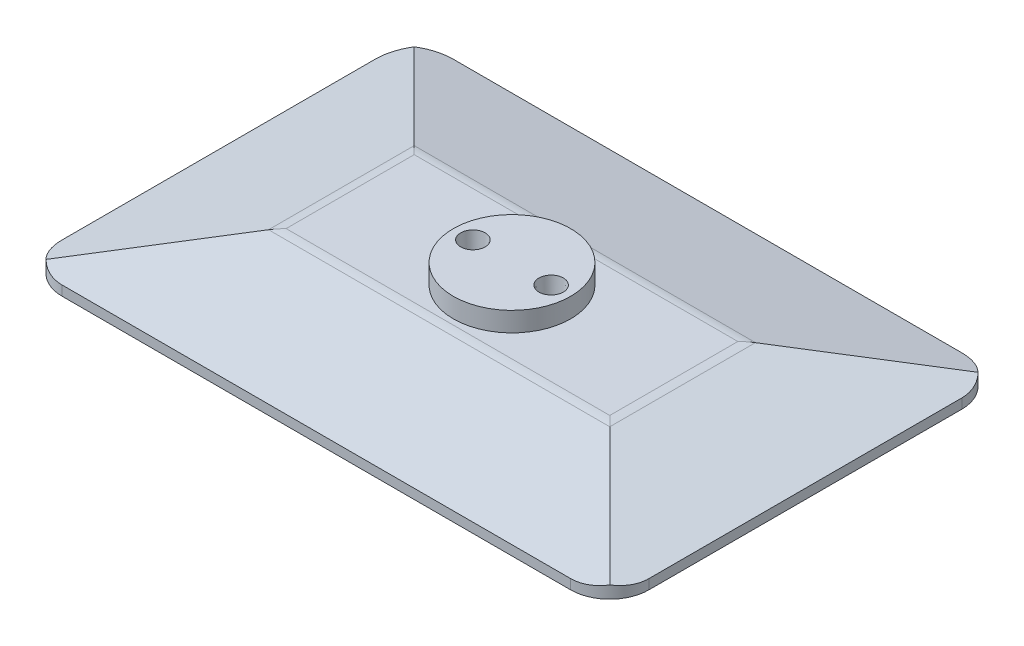
SolidWorks part; units mm, degrees
ref_plane "前视基准面" through (0, 0, 0) normal (0, 0, 1) x (1, 0, 0)
ref_plane "上视基准面" through (0, 0, 0) normal (0, 1, 0) x (1, 0, 0)
ref_plane "右视基准面" through (0, 0, 0) normal (1, 0, 0) x (0, 0, -1)
other "Configuration Table"
sketch "草图1" plane through (0, 0, 0) normal (0, 1, 0) x (1, 0, 0)
  line L0 (-48.5913, -10.2137) -> (-40.6154, -10.2137) construction
  line L1 (-33.5732, -10.2137) -> (-35.5732, -10.2137) construction
  line L2 (5.9754, 18.7871) -> (5.9754, 46.3845) construction
  line L3 (5.9754, 9.5066) -> (5.9754, -30.4934) construction
  line L5 (-24.0246, 9.7863) -> (35.9754, 9.7863)
  line L6 (-24.0246, 9.7863) -> (-24.0246, -30.2137)
  line L7 (-24.0246, -30.2137) -> (35.9754, -30.2137)
  line L8 (35.9754, 9.7863) -> (35.9754, -30.2137)
  line L9 (-24.0246, 9.7863) -> (35.9754, -30.2137) construction
  line L10 (-24.0246, -30.2137) -> (35.9754, 9.7863) construction
  point P8 (5.9754, -10.2137)
  dimension "D1" = 60
  dimension "D2" = 40
extrude "凸台-拉伸1" add sketch "草图1" along normal blind 1
sketch "草图2" plane through (0, 1, 0) normal (0, 1, 0) x (1, 0, 0)
  line L4 (35.9754, -30.2137) -> (35.9754, 9.7863)
  line L5 (35.9754, 9.7863) -> (-24.0246, 9.7863)
  line L6 (-24.0246, 9.7863) -> (-24.0246, -30.2137)
  line L7 (-24.0246, -30.2137) -> (35.9754, -30.2137)
  line L8 (35.9754, -30.2137) -> (35.9754, 9.7863)
  line L9 (35.9754, 9.7863) -> (-24.0246, 9.7863)
  line L10 (-24.0246, 9.7863) -> (-24.0246, -30.2137)
  line L11 (-24.0246, -30.2137) -> (35.9754, -30.2137)
  dimension "D1" = 0
extrude "凸台-拉伸2" add sketch "草图2" along normal blind 3 draft 77
fillet "圆角1" radius 4 4 edges at (-24.0246, 0.5, -9.7863) (35.9754, 0.5, -9.7863) (35.9754, 0.5, 30.2137) (-24.0246, 0.5, 30.2137)
sketch "草图3" plane through (0, 4, 0) normal (0, 1, 0) x (1, 0, 0)
  line L1 (5.9754, -16.2137) -> (5.9754, -4.2137) construction
  circle A0 centre (5.9754, -10.2137) radius 6
  dimension "D1" = 12
extrude "凸台-拉伸3" add sketch "草图3" along normal blind 2
fillet "圆角2" radius 4 4 edges at (22.9809, 4, 10.2137) (5.9754, 4, 3.2082) (-11.0302, 4, 10.2137) (5.9754, 4, 17.2193)
sketch "草图4" plane through (0, 6, 0) normal (0, 1, 0) x (1, 0, 0)
  line L0 (6.7345, -10.2137) -> (29.8962, -10.2137) construction
  line L2 (5.9754, 14.4249) -> (5.9754, 22.7292) construction
  line L3 (5.9754, -16.2137) -> (5.9754, -4.2137) construction
  circle A1 centre (1.9754, -10.2137) radius 1.25
  circle A3 centre (9.9754, -10.2137) radius 1.25
  circle A5 centre (5.9754, -6.2137) radius 1.25 [skipped]
  circle A6 centre (5.9754, -14.2137) radius 1.25 [skipped]
  point P17 (5.9754, -10.2137)
  dimension "D1" = 2.5
  dimension "D3" = 4
  dimension "D2" = 4
extrude "切除-拉伸1" cut sketch "草图4" against normal blind 3 draft 5
